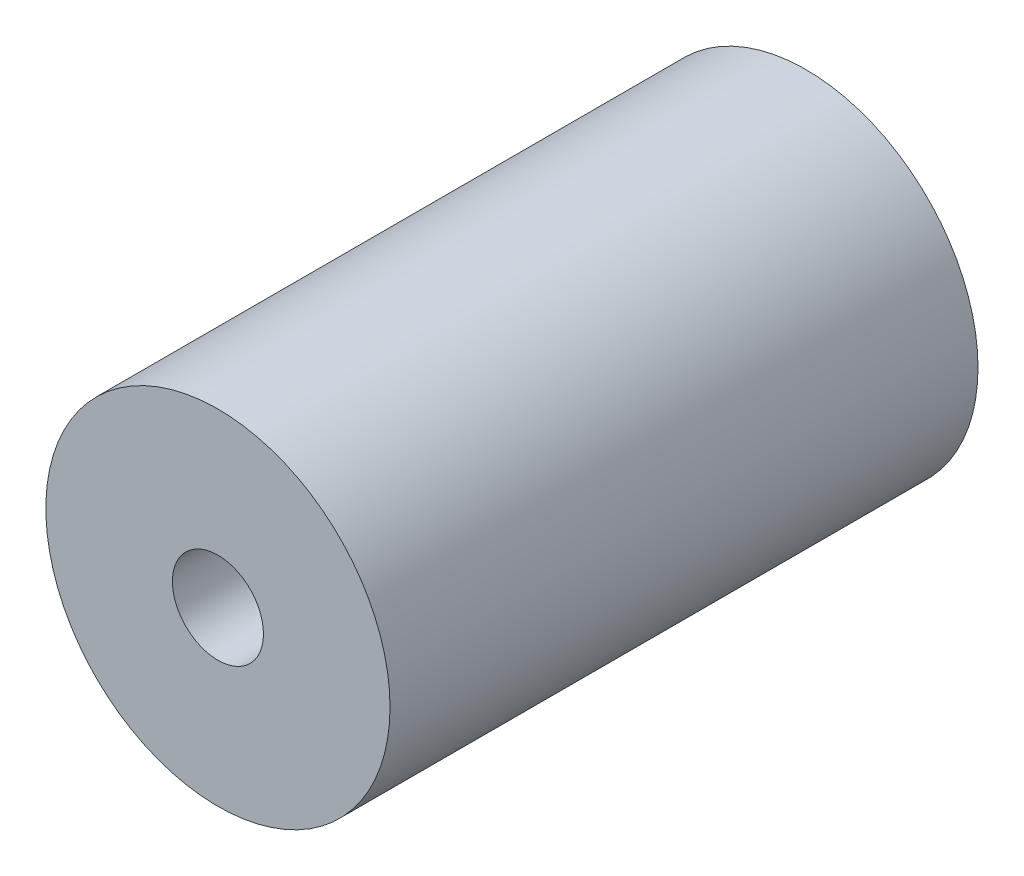
SolidWorks part; units mm, degrees
ref_plane "Front Plane" through (0, 0, 0) normal (0, 0, 1) x (1, 0, 0)
ref_plane "Top Plane" through (0, 0, 0) normal (0, 1, 0) x (1, 0, 0)
ref_plane "Right Plane" through (0, 0, 0) normal (1, 0, 0) x (0, 0, -1)
sketch "Sketch1" plane through (0, 0, 0) normal (0, 0, 1) x (1, 0, 0)
  circle A0 centre (-4.3781, 5.745) radius 6
  circle A1 centre (-4.3781, 5.745) radius 1.5875
  dimension "D1" = 12
  dimension "D2" = 3.175
extrude "Boss-Extrude1" add sketch "Sketch1" along normal blind 10.5 and the other way blind 10
